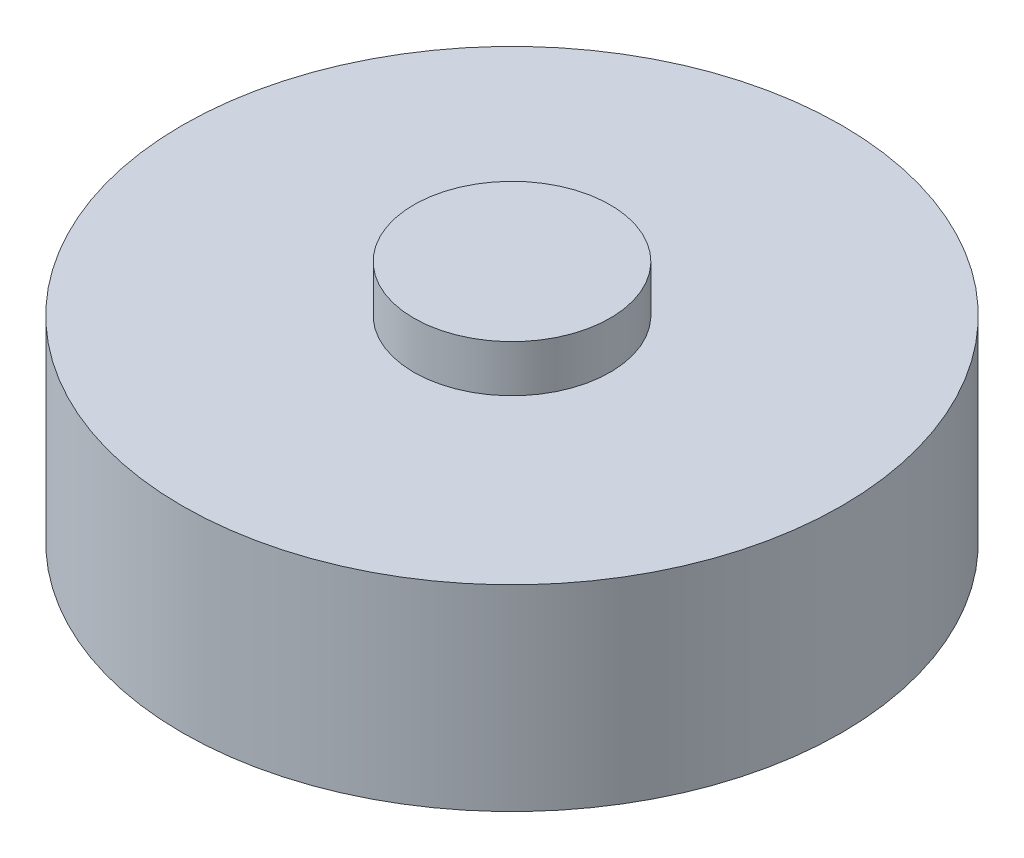
SolidWorks part; units mm, degrees
ref_plane "Front Plane" through (0, 0, 0) normal (0, 0, 1) x (1, 0, 0)
ref_plane "Top Plane" through (0, 0, 0) normal (0, 1, 0) x (1, 0, 0)
ref_plane "Right Plane" through (0, 0, 0) normal (1, 0, 0) x (0, 0, -1)
sketch "Sketch1" plane through (0, 0, 0) normal (0, 1, 0) x (1, 0, 0)
  circle A0 centre (0, 0) radius 29.845
  dimension "D1" = 59.69
extrude "Boss-Extrude1" add sketch "Sketch1" along normal blind 17.78
sketch "Sketch2" plane through (0, 17.78, 0) normal (0, 1, 0) x (1, 0, 0)
  circle A0 centre (0, 0) radius 8.89
  dimension "D1" = 17.78
extrude "Boss-Extrude2" add sketch "Sketch2" along normal blind 4.2418
sketch "Sketch3" plane through (0, 0, 0) normal (0, -1, 0) x (-1, 0, 0)
  circle A0 centre (0, 0) radius 7.493
  dimension "D1" = 14.986
extrude "Boss-Extrude3" add sketch "Sketch3" along normal blind 4.064
sketch "Sketch4" plane through (0, -4.064, 0) normal (0, -1, 0) x (1, 0, 0)
  circle A0 centre (0, 0) radius 8.255
  dimension "D1" = 16.51
extrude "Boss-Extrude4" add sketch "Sketch4" along normal blind 0.762
sketch "Sketch6" plane through (0, -4.826, 0) normal (0, -1, 0) x (-1, 0, 0)
  line L0 (-2.3383, -1.35) -> (2.3383, -1.35)
  line L1 (-2.3383, 1.35) -> (2.3383, 1.35)
  arc A0 (2.3383, -1.35) -> (2.3383, 1.35) centre (0, 0) ccw
  arc A2 (-2.3383, 1.35) -> (-2.3383, -1.35) centre (0, 0) ccw
  circle A3 centre (0, 0) radius 0.95
extrude "Cut-Extrude1" cut sketch "Sketch6" against normal blind 25.4
